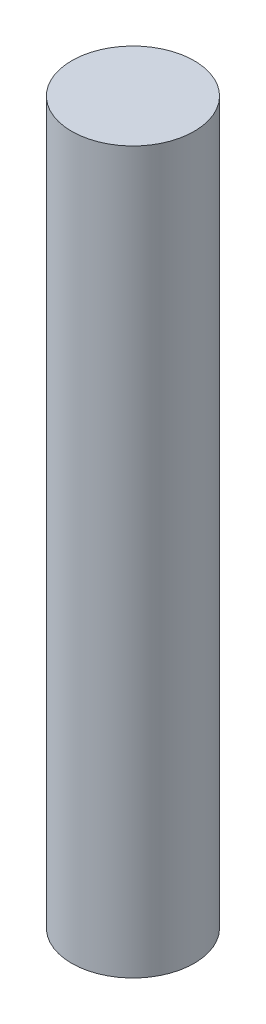
SolidWorks part; units mm, degrees
ref_plane "Front Plane" through (0, 0, 0) normal (0, 0, 1) x (1, 0, 0)
ref_plane "Top Plane" through (0, 0, 0) normal (0, 1, 0) x (1, 0, 0)
ref_plane "Right Plane" through (0, 0, 0) normal (1, 0, 0) x (0, 0, -1)
sketch "Sketch1" plane through (0, 0, 0) normal (0, 1, 0) x (1, 0, 0)
  circle A0 centre (0, 0) radius 8.5
  dimension "D1" = 17
extrude "Boss-Extrude1" add sketch "Sketch1" along normal blind 100
sketch "Sketch2" plane through (0, 0, 0) normal (0, -1, 0) x (1, 0, 0)
  circle A0 centre (0, 0) radius 10.5
  dimension "D1" = 21
